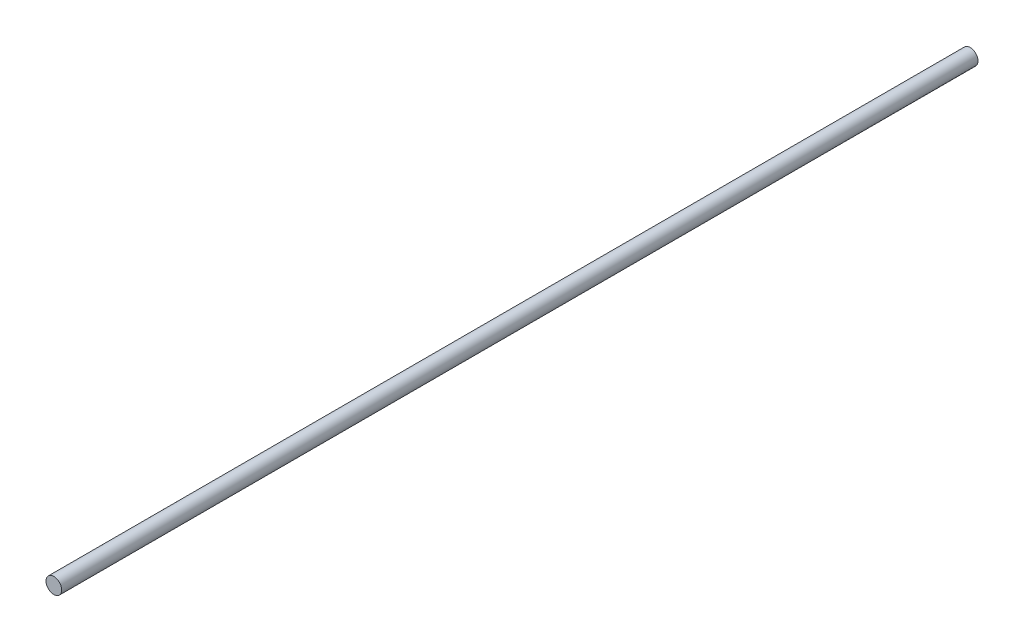
SolidWorks part; units mm, degrees
ref_plane "Front Plane" through (0, 0, 0) normal (0, 0, 1) x (1, 0, 0)
ref_plane "Top Plane" through (0, 0, 0) normal (0, 1, 0) x (1, 0, 0)
ref_plane "Right Plane" through (0, 0, 0) normal (1, 0, 0) x (0, 0, -1)
sketch "Sketch1" plane through (0, 0, 0) normal (0, 0, 1) x (1, 0, 0)
  circle A0 centre (0, 0) radius 3.175
  dimension "D1" = 6.35
extrude "Boss-Extrude1" add sketch "Sketch1" along normal blind 370.84
